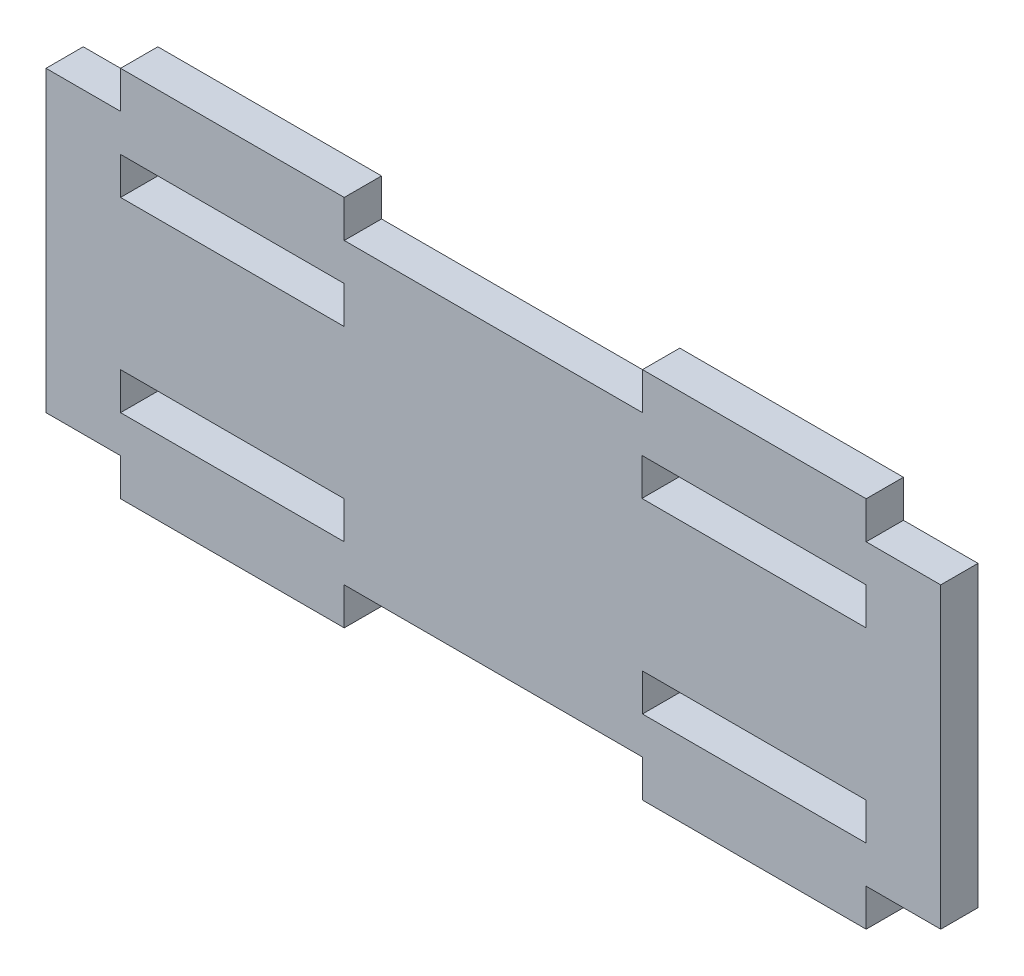
SolidWorks part; units mm, degrees
ref_plane "Front Plane" through (0, 0, 0) normal (0, 0, 1) x (1, 0, 0)
ref_plane "Top Plane" through (0, 0, 0) normal (0, 1, 0) x (1, 0, 0)
ref_plane "Right Plane" through (0, 0, 0) normal (1, 0, 0) x (0, 0, -1)
sketch "Sketch1" plane through (0, 0, 0) normal (0, 0, 1) x (1, 0, 0)
  line L0 (-50, 20) -> (-50, -20) construction
  line L1 (-60, 20) -> (60, 20)
  line L2 (-60, 20) -> (-60, -20)
  line L3 (-60, -20) -> (60, -20)
  line L4 (60, 20) -> (60, -20)
  line L5 (-60, 20) -> (60, -20) construction
  line L6 (-60, -20) -> (60, 20) construction
  line L7 (-50, 20) -> (-20, 20)
  line L8 (-50, 20) -> (-50, 25)
  line L9 (-50, 25) -> (-20, 25)
  line L10 (-20, 20) -> (-20, 25)
  line L11 (20, 20) -> (50, 20)
  line L12 (20, 20) -> (20, 25)
  line L13 (20, 25) -> (50, 25)
  line L14 (50, 20) -> (50, 25)
  line L15 (-50, -20) -> (-20, -20)
  line L16 (-50, -20) -> (-50, -25)
  line L17 (-50, -25) -> (-20, -25)
  line L18 (-20, -20) -> (-20, -25)
  line L19 (20, -20) -> (50, -20)
  line L20 (20, -20) -> (20, -25)
  line L21 (20, -25) -> (50, -25)
  line L22 (50, -20) -> (50, -25)
  line L23 (-50, 15) -> (-20, 15)
  line L24 (-50, 15) -> (-50, 10)
  line L25 (-50, 10) -> (-20, 10)
  line L26 (-20, 15) -> (-20, 10)
  line L27 (-50, -10) -> (-20, -10)
  line L28 (-50, -10) -> (-50, -15)
  line L29 (-50, -15) -> (-20, -15)
  line L30 (-20, -10) -> (-20, -15)
  line L31 (20, -10) -> (50, -10)
  line L32 (20, -10) -> (20, -15)
  line L33 (20, -15) -> (50, -15)
  line L34 (50, -10) -> (50, -15)
  line L35 (19.9199, 10) -> (49.993, 10)
  line L36 (19.9199, 10) -> (19.9199, 15)
  line L37 (19.9199, 15) -> (49.993, 15)
  line L38 (49.993, 10) -> (49.993, 15)
  line L39 (-20, 20) -> (-20, -20) construction
  line L40 (20, 20) -> (20, -20) construction
  line L41 (50, 20) -> (50, -20) construction
  point P0 (0, 0)
  point P38 (50, -12.5)
  point P43 (-20, -22.5)
  dimension "D1" = 10
  dimension "D2" = 30
  dimension "D3" = 40
  dimension "D4" = 30
  dimension "D5" = 40
  dimension "D6" = 10
  dimension "D7" = 5
  dimension "D8" = 5
  dimension "D9" = 5
  dimension "D10" = 5
  dimension "D11" = 0
  dimension "D12" = 0
  dimension "D13" = 0
  dimension "D14" = 0
  dimension "D15" = 0
  dimension "D16" = 0
  dimension "D17" = 0
  dimension "D18" = 0
  dimension "D19" = 5
  dimension "D20" = 5
  dimension "D21" = 5
  dimension "D22" = 5
  dimension "D23" = 0
  dimension "D24" = 0
  dimension "D25" = 5
  dimension "D26" = 20
  dimension "D27" = 5
  dimension "D28" = 20
extrude "Boss-Extrude1" add sketch "Sketch1" along normal blind 5 contours L4 L1 L2 L3 L38 L35 L36 L37 L23 L26 L25 L24 L27 L30 L29 L28 L31 L34 L33 L32 | L18 L3 L16 L17 | L22 L3 L20 L21 | L1 L14 L13 L12 | L1 L10 L9 L8
